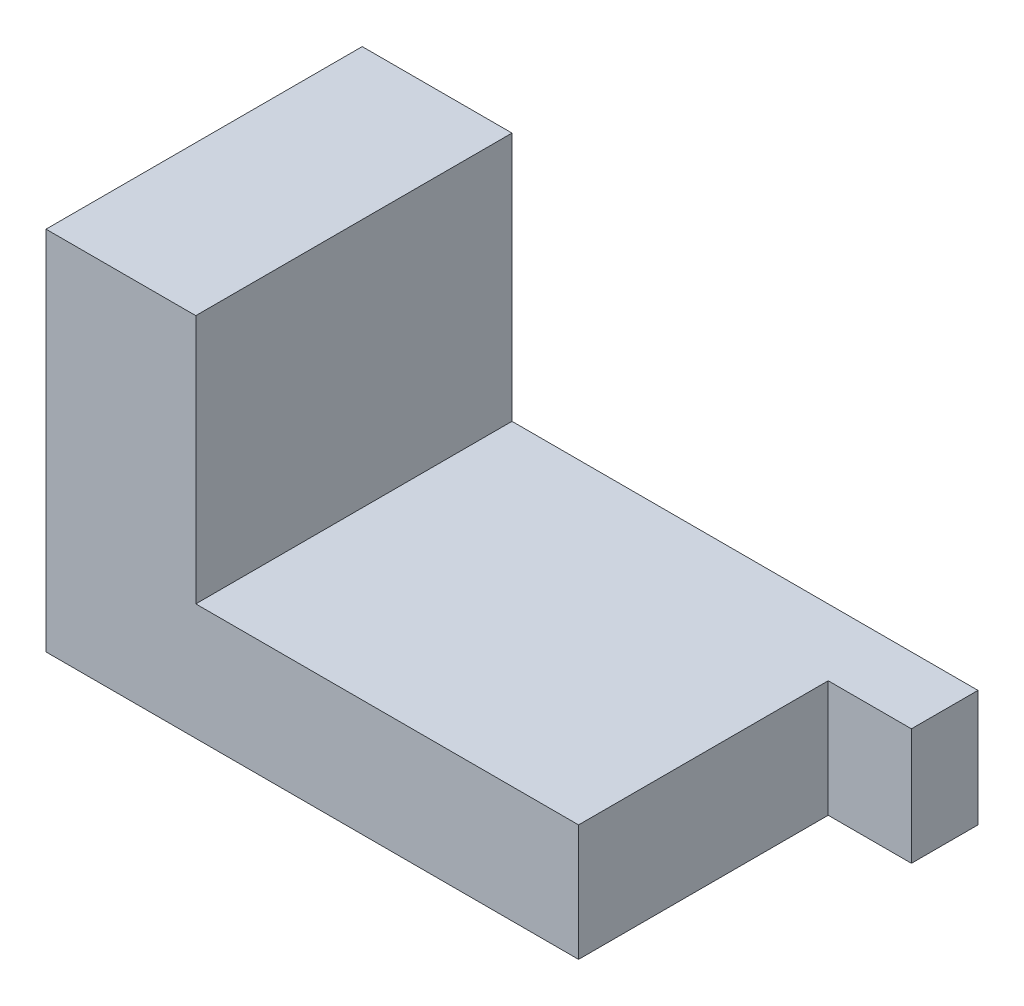
SolidWorks part; units mm, degrees
ref_plane "Front Plane" through (0, 0, 0) normal (0, 0, 1) x (1, 0, 0)
ref_plane "Top Plane" through (0, 0, 0) normal (0, 1, 0) x (1, 0, 0)
ref_plane "Right Plane" through (0, 0, 0) normal (1, 0, 0) x (0, 0, -1)
sketch "Sketch1" plane through (0, 0, 0) normal (0, 1, 0) x (1, 0, 0)
  line L1 (-16, 9.5) -> (16, 9.5)
  line L2 (-16, 9.5) -> (-16, -9.5)
  line L3 (-16, -9.5) -> (16, -9.5)
  line L4 (16, 9.5) -> (16, -9.5)
  line L5 (-16, 9.5) -> (16, -9.5) construction
  line L6 (-16, -9.5) -> (16, 9.5) construction
  point P0 (0, 0)
  dimension "D1" = 19
  dimension "D2" = 32
extrude "Boss-Extrude1" add sketch "Sketch1" along normal blind 7
sketch "Sketch2" plane through (0, 7, 0) normal (0, 1, 0) x (1, 0, 0)
  line L0 (-16, -9.5) -> (16, -9.5) construction
  line L1 (-16, 9.5) -> (-7, 9.5)
  line L2 (-16, 9.5) -> (-16, -9.5)
  line L3 (-16, -9.5) -> (-7, -9.5)
  line L4 (-7, 9.5) -> (-7, -9.5)
  dimension "D1" = 9
extrude "Boss-Extrude2" add sketch "Sketch2" along normal blind 15
sketch "Sketch3" plane through (16, 0, 0) normal (1, 0, 0) x (0, 0, -1)
  line L0 (-9.5, 0) -> (9.5, 0) construction
  line L1 (9.5, 7) -> (5.5, 7)
  line L2 (9.5, 7) -> (9.5, 0)
  line L3 (9.5, 0) -> (5.5, 0)
  line L4 (5.5, 7) -> (5.5, 0)
  dimension "D1" = 4
extrude "Boss-Extrude3" add sketch "Sketch3" along normal blind 5
